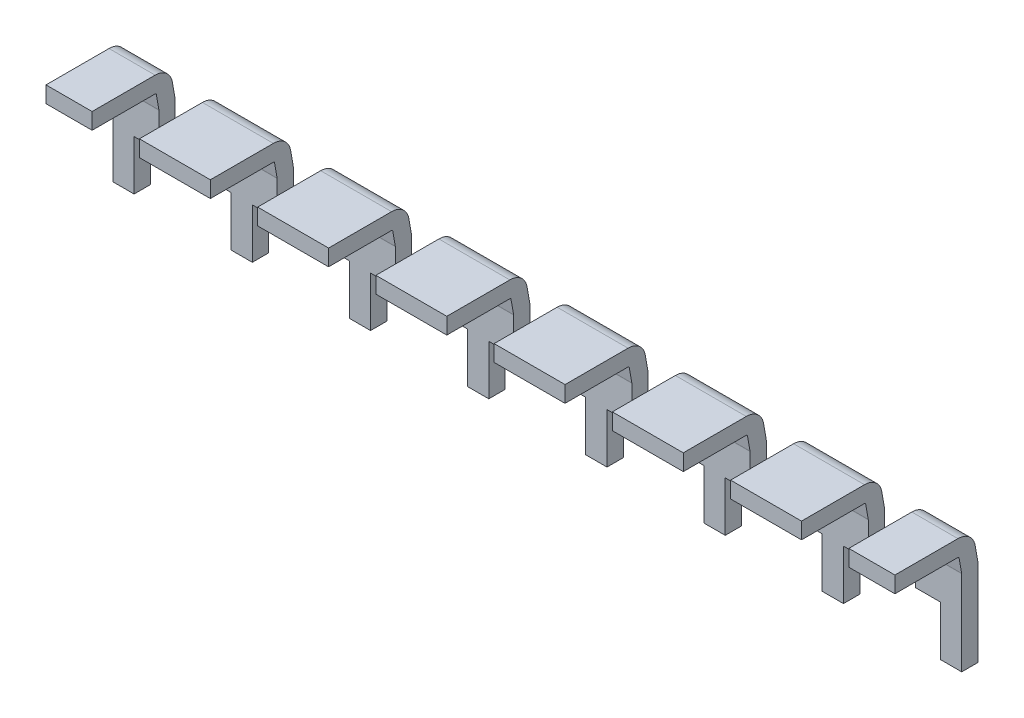
SolidWorks part; units mm, degrees
ref_plane "Front Plane" through (0, 0, 0) normal (0, 0, 1) x (1, 0, 0)
ref_plane "Top Plane" through (0, 0, 0) normal (0, 1, 0) x (1, 0, 0)
ref_plane "Right Plane" through (0, 0, 0) normal (1, 0, 0) x (0, 0, -1)
sketch "Sketch1" plane through (0, 0, 0) normal (0, 0, 1) x (1, 0, 0)
  line L0 (8.128, 0.175) -> (9.652, 0.175) construction
  line L1 (-2.032, 0.175) -> (-0.508, 0.175)
  line L2 (-2.032, 0.175) -> (-2.032, -0.175)
  line L3 (-2.032, -0.175) -> (-0.508, -0.175)
  line L4 (-0.508, 0.175) -> (-0.508, -0.175)
  line L5 (-2.032, 0.175) -> (-0.508, -0.175) construction
  line L6 (-2.032, -0.175) -> (-0.508, 0.175) construction
  line L7 (5.588, 0.175) -> (7.112, 0.175)
  line L8 (5.588, 0.175) -> (5.588, -0.175)
  line L9 (5.588, -0.175) -> (7.112, -0.175)
  line L10 (7.112, 0.175) -> (7.112, -0.175)
  line L11 (5.588, 0.175) -> (7.112, -0.175) construction
  line L12 (5.588, -0.175) -> (7.112, 0.175) construction
  line L13 (8.128, 0.175) -> (8.128, -0.175)
  line L14 (8.128, -0.175) -> (9.652, -0.175) construction
  line L15 (9.652, 0.175) -> (9.652, -0.175) construction
  line L16 (8.128, 0.175) -> (9.652, -0.175) construction
  line L17 (8.128, -0.175) -> (9.652, 0.175) construction
  line L18 (-9.652, 0.175) -> (-8.128, 0.175) construction
  line L19 (-9.652, 0.175) -> (-9.652, -0.175) construction
  line L20 (-9.652, -0.175) -> (-8.128, -0.175) construction
  line L21 (-8.128, 0.175) -> (-8.128, -0.175)
  line L22 (-9.652, 0.175) -> (-8.128, -0.175) construction
  line L23 (-9.652, -0.175) -> (-8.128, 0.175) construction
  line L24 (-9.1186, 0.175) -> (-9.1186, -0.175)
  line L25 (9.1186, 0.175) -> (9.1186, -0.175)
  line L26 (9.1186, 0.175) -> (8.128, 0.175)
  line L27 (9.1186, -0.175) -> (8.128, -0.175)
  line L28 (-8.128, 0.175) -> (-9.1186, 0.175)
  line L29 (-8.128, -0.175) -> (-9.1186, -0.175)
  line L30 (-4.572, 0.175) -> (-3.048, 0.175)
  line L31 (-4.572, 0.175) -> (-4.572, -0.175)
  line L32 (-4.572, -0.175) -> (-3.048, -0.175)
  line L33 (-3.048, 0.175) -> (-3.048, -0.175)
  line L34 (-4.572, 0.175) -> (-3.048, -0.175) construction
  line L35 (-4.572, -0.175) -> (-3.048, 0.175) construction
  line L36 (-7.112, 0.175) -> (-5.588, 0.175)
  line L37 (-7.112, 0.175) -> (-7.112, -0.175)
  line L38 (-7.112, -0.175) -> (-5.588, -0.175)
  line L39 (-5.588, 0.175) -> (-5.588, -0.175)
  line L40 (-7.112, 0.175) -> (-5.588, -0.175) construction
  line L41 (-7.112, -0.175) -> (-5.588, 0.175) construction
  line L42 (0.508, 0.175) -> (2.032, 0.175)
  line L43 (0.508, 0.175) -> (0.508, -0.175)
  line L44 (0.508, -0.175) -> (2.032, -0.175)
  line L45 (2.032, 0.175) -> (2.032, -0.175)
  line L46 (0.508, 0.175) -> (2.032, -0.175) construction
  line L47 (0.508, -0.175) -> (2.032, 0.175) construction
  line L48 (3.048, 0.175) -> (4.572, 0.175)
  line L49 (3.048, 0.175) -> (3.048, -0.175)
  line L50 (3.048, -0.175) -> (4.572, -0.175)
  line L51 (4.572, 0.175) -> (4.572, -0.175)
  line L52 (3.048, 0.175) -> (4.572, -0.175) construction
  line L53 (3.048, -0.175) -> (4.572, 0.175) construction
  point P0 (-1.27, 0)
  point P5 (6.35, 0)
  point P12 (8.89, 0)
  point P17 (-8.89, 0)
  point P26 (-3.81, 0)
  point P31 (-6.35, 0)
  point P36 (1.27, 0)
  point P41 (3.81, 0)
  dimension "D1" = 1.524
  dimension "D2" = 7.62
  dimension "D3" = 1.524
  dimension "D4" = 1.27
  dimension "D5" = 0.35
  dimension "D6" = 0.5334
  dimension "D7" = 0.5334
  dimension "D8" = 7.62
  dimension "D9" = 2.54
  dimension "D10" = 2.54
  dimension "D11" = 2.54
sketch "Sketch2" plane through (0, 0, 0) normal (1, 0, 0) x (0, 0, -1)
  line L0 (0, 0) -> (1.354, 0)
  line L1 (1.61, -0.5175) -> (1.61, -2.345)
  line L2 (1.607, -0.4828) -> (1.551, -0.1653)
  arc A0 (1.354, 0) -> (1.551, -0.1653) centre (1.354, -0.2) cw
  arc A1 (1.607, -0.4828) -> (1.61, -0.5175) centre (1.41, -0.5175) cw
  point P10 (1.61, -0.5)
  dimension "D5" = 0.2
  dimension "D6" = 0.2
  dimension "D1" = 1.61
  dimension "D2" = 10
  dimension "D3" = 1.845
  dimension "D4" = 0.5
sweep "Sweep11" add profiles "Sketch1" path "Sketch2"
sketch "Sketch10" plane through (0, 0.2906, -1.6483) normal (0, 0.1736, -0.9848) x (-1, 0, 0)
  line L0 (-9.1186, -0.7545) -> (-8.128, -0.7545) construction
  line L1 (-8.6614, -1.5045) -> (-8.128, -1.5045)
  line L2 (-8.6614, -1.5045) -> (-8.6614, -2.6193)
  line L3 (-8.6614, -2.6193) -> (-8.128, -2.6193)
  line L4 (-8.128, -1.5045) -> (-8.128, -2.6193)
  line L5 (-8.6614, -1.5045) -> (-8.128, -2.6193) construction
  line L6 (-8.6614, -2.6193) -> (-8.128, -1.5045) construction
  line L8 (-7.112, -1.5045) -> (-6.5786, -1.5045)
  line L9 (-7.112, -1.5045) -> (-7.112, -2.6193)
  line L10 (-7.112, -2.6193) -> (-6.5786, -2.6193)
  line L11 (-5.588, -1.5045) -> (-5.588, -2.6193)
  line L12 (-7.112, -1.5045) -> (-5.588, -2.6193) construction
  line L13 (-7.112, -2.6193) -> (-5.588, -1.5045) construction
  line L14 (-4.572, -1.5045) -> (-4.0386, -1.5045)
  line L15 (-4.572, -1.5045) -> (-4.572, -2.6193)
  line L16 (-4.572, -2.6193) -> (-4.0386, -2.6193)
  line L17 (-3.048, -1.5045) -> (-3.048, -2.6193)
  line L18 (-4.0386, -1.5045) -> (-4.0386, -2.6193)
  line L19 (-3.5814, -1.5045) -> (-3.5814, -2.6193)
  line L20 (8.6614, -1.5045) -> (8.128, -1.5045)
  line L21 (8.6614, -1.5045) -> (8.6614, -2.6193)
  line L22 (8.6614, -2.6193) -> (8.128, -2.6193)
  line L23 (8.128, -1.5045) -> (8.128, -2.6193)
  line L24 (8.6614, -1.5045) -> (8.128, -2.6193) construction
  line L25 (8.6614, -2.6193) -> (8.128, -1.5045) construction
  line L28 (-7.112, -0.8196) -> (-7.112, -2.6193) construction
  line L32 (-6.5786, -1.5045) -> (-6.5786, -2.6193)
  line L33 (-6.1214, -1.5045) -> (-6.1214, -2.6193)
  line L34 (-3.5814, -1.5045) -> (-3.048, -1.5045)
  line L35 (-3.5814, -2.6193) -> (-3.048, -2.6193)
  line L36 (-6.1214, -1.5045) -> (-5.588, -1.5045)
  line L37 (-6.1214, -2.6193) -> (-5.588, -2.6193)
  line L38 (-4.572, -1.5045) -> (-3.048, -2.6193) construction
  line L39 (-4.572, -2.6193) -> (-3.048, -1.5045) construction
  line L41 (-8.128, -0.8196) -> (-8.128, -2.6193) construction
  line L42 (8.128, -0.8196) -> (8.128, -2.6193) construction
  line L43 (8.128, -2.6193) -> (9.1186, -2.6193) construction
  line L44 (-9.1186, -2.6193) -> (-8.128, -2.6193) construction
  line L45 (-2.032, -1.5045) -> (-1.4986, -1.5045)
  line L46 (-2.032, -1.5045) -> (-2.032, -2.6193)
  line L47 (-2.032, -2.6193) -> (-1.4986, -2.6193)
  line L48 (-0.508, -1.5045) -> (-0.508, -2.6193)
  line L49 (-1.4986, -1.5045) -> (-1.4986, -2.6193)
  line L50 (-1.0414, -1.5045) -> (-1.0414, -2.6193)
  line L51 (-1.0414, -1.5045) -> (-0.508, -1.5045)
  line L52 (-1.0414, -2.6193) -> (-0.508, -2.6193)
  line L53 (-2.032, -1.5045) -> (-0.508, -2.6193) construction
  line L54 (-2.032, -2.6193) -> (-0.508, -1.5045) construction
  line L55 (0.508, -1.5045) -> (1.0414, -1.5045)
  line L56 (0.508, -1.5045) -> (0.508, -2.6193)
  line L57 (0.508, -2.6193) -> (1.0414, -2.6193)
  line L58 (2.032, -1.5045) -> (2.032, -2.6193)
  line L59 (1.0414, -1.5045) -> (1.0414, -2.6193)
  line L60 (1.4986, -1.5045) -> (1.4986, -2.6193)
  line L61 (1.4986, -1.5045) -> (2.032, -1.5045)
  line L62 (1.4986, -2.6193) -> (2.032, -2.6193)
  line L63 (0.508, -1.5045) -> (2.032, -2.6193) construction
  line L64 (0.508, -2.6193) -> (2.032, -1.5045) construction
  line L65 (3.048, -1.5045) -> (3.5814, -1.5045)
  line L66 (3.048, -1.5045) -> (3.048, -2.6193)
  line L67 (3.048, -2.6193) -> (3.5814, -2.6193)
  line L68 (4.572, -1.5045) -> (4.572, -2.6193)
  line L69 (3.5814, -1.5045) -> (3.5814, -2.6193)
  line L70 (4.0386, -1.5045) -> (4.0386, -2.6193)
  line L71 (4.0386, -1.5045) -> (4.572, -1.5045)
  line L72 (4.0386, -2.6193) -> (4.572, -2.6193)
  line L73 (3.048, -1.5045) -> (4.572, -2.6193) construction
  line L74 (3.048, -2.6193) -> (4.572, -1.5045) construction
  line L75 (5.588, -1.5045) -> (6.1214, -1.5045)
  line L76 (5.588, -1.5045) -> (5.588, -2.6193)
  line L77 (5.588, -2.6193) -> (6.1214, -2.6193)
  line L78 (7.112, -1.5045) -> (7.112, -2.6193)
  line L79 (6.1214, -1.5045) -> (6.1214, -2.6193)
  line L80 (6.5786, -1.5045) -> (6.5786, -2.6193)
  line L81 (6.5786, -1.5045) -> (7.112, -1.5045)
  line L82 (6.5786, -2.6193) -> (7.112, -2.6193)
  line L83 (5.588, -1.5045) -> (7.112, -2.6193) construction
  line L84 (5.588, -2.6193) -> (7.112, -1.5045) construction
  point P0 (-8.3947, -2.0619)
  point P5 (-8.6233, -0.7545)
  point P6 (-6.35, -2.0619)
  point P16 (-3.81, -2.0619)
  point P21 (8.3947, -2.0619)
  point P44 (-1.27, -2.0619)
  point P55 (1.27, -2.0619)
  point P64 (3.81, -2.0619)
  point P73 (6.35, -2.0619)
  dimension "D1" = 0.5334
  dimension "D2" = 0.5334
  dimension "D3" = 0.4572
  dimension "D4" = 2.54
  dimension "D5" = 0.75
  dimension "D6" = 0.2286
extrude "Extrude1" cut sketch "Sketch10" against normal through all
